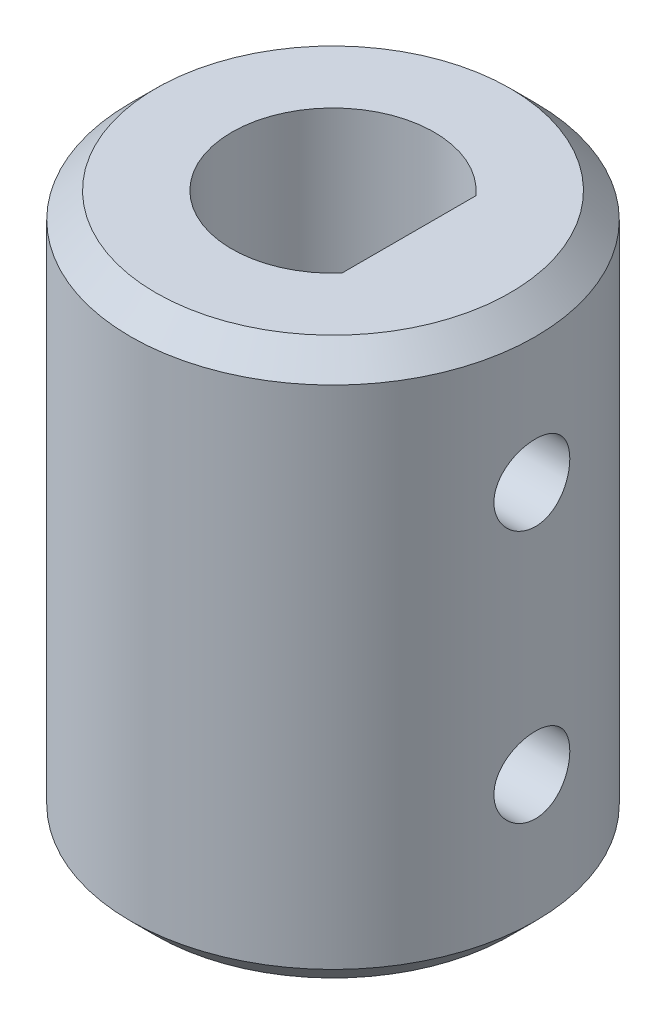
SolidWorks part; units mm, degrees
ref_plane "Front Plane" through (0, 0, 0) normal (0, 0, 1) x (1, 0, 0)
ref_plane "Top Plane" through (0, 0, 0) normal (0, 1, 0) x (1, 0, 0)
ref_plane "Right Plane" through (0, 0, 0) normal (1, 0, 0) x (0, 0, -1)
sketch "Sketch1" plane through (0, 0, 0) normal (0, 1, 0) x (1, 0, 0)
  circle A0 centre (0, 0) radius 8
  dimension "D1" = 16
extrude "Boss-Extrude1" add sketch "Sketch1" along normal blind 22
sketch "Sketch2" plane through (0, 22, 0) normal (0, 1, 0) x (1, 0, 0)
  line L0 (3, 2.6458) -> (3, -2.6458)
  arc A0 (0, 4) -> (0, -4) centre (0, 0) ccw
  arc A1 (0, 4) -> (3, 2.6458) centre (0, 0) cw
  arc A2 (3, -2.6458) -> (0, -4) centre (0, 0) cw
  dimension "D1" = 8
  dimension "D2" = 3
sketch "Sketch3" plane through (0, 0, 0) normal (0, -1, 0) x (1, 0, 0)
  line L0 (0, -4) -> (0, 4) construction
  line L1 (3, 2.6458) -> (3, -2.6458)
  arc A0 (3, 2.6458) -> (3, -2.6458) centre (0, 0) ccw
  dimension "D1" = 8
  dimension "D2" = 3
extrude "Cut-Extrude3" cut sketch "Sketch3" against normal blind 12 contours A0 L1
extrude "Cut-Extrude4" cut sketch "Sketch2" against normal blind 10
chamfer "Chamfer1" distance 1 angle 45 2 edges at (0, 0, 8) (0, 22, 8)
ref_plane "Plane1" through (8, 0, 0) normal (1, 0, 0) x (0, 0, -1)
sketch "Sketch4" plane through (8, 0, 0) normal (1, 0, 0) x (0, 0, -1)
  line L0 (0, 22) -> (0, 16) construction
  line L1 (-2.6458, 22) -> (2.6458, 22) construction
  line L2 (-8, 11) -> (8, 11) construction
  line L3 (-8, 21) -> (-8, 1) construction
  line L4 (8, 1) -> (8, 21) construction
  circle A0 centre (0, 16) radius 1.5
  circle A1 centre (0, 6) radius 1.5
  dimension "D2" = 3
  dimension "D1" = 6
extrude "Cut-Extrude5" cut sketch "Sketch4" against normal up to next
